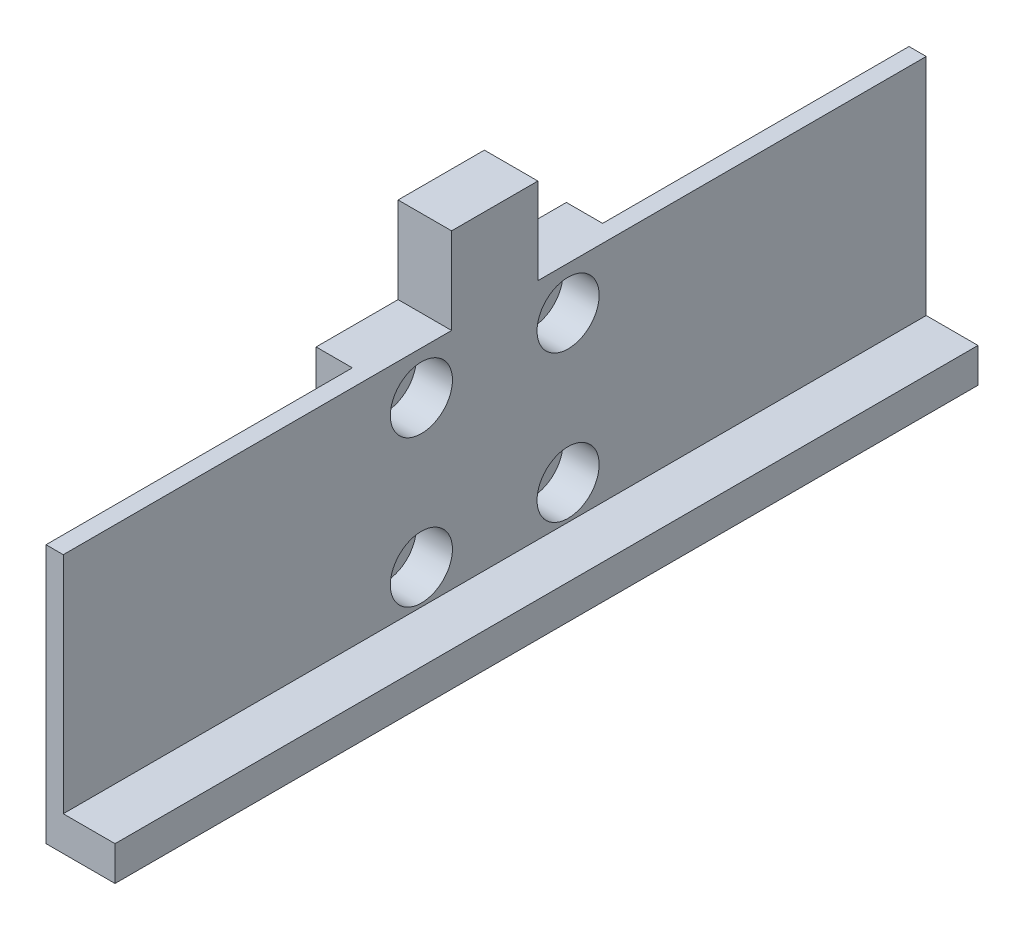
SolidWorks part; units mm, degrees
ref_plane "Front Plane" through (0, 0, 0) normal (0, 0, 1) x (1, 0, 0)
ref_plane "Top Plane" through (0, 0, 0) normal (0, 1, 0) x (1, 0, 0)
ref_plane "Right Plane" through (0, 0, 0) normal (1, 0, 0) x (0, 0, -1)
sketch "Sketch1" plane through (0, 0, 0) normal (1, 0, 0) x (0, 0, -1)
  line L1 (0, 0) -> (100, 0)
  line L2 (0, 0) -> (0, 26)
  line L3 (0, 26) -> (100, 26)
  line L4 (100, 0) -> (100, 26)
  dimension "D1" = 100
  dimension "D2" = 26
extrude "Boss-Extrude1" add sketch "Sketch1" along normal blind 2
sketch "Sketch2" plane through (0, 0, 0) normal (0, 0, 1) x (1, 0, 0)
  line L0 (2, 26) -> (2, 28)
  line L1 (2, 28) -> (-12, 28)
  line L2 (-12, 28) -> (-12, 24)
  line L3 (-12, 24) -> (-10, 24)
  line L4 (-10, 24) -> (-10, 26)
  line L5 (-10, 26) -> (2, 26)
  line L6 (2, 0) -> (0, 0) construction
  line L7 (0, 26) -> (0, 0) construction
  dimension "D1" = 10
  dimension "D2" = 2
extrude "Boss-Extrude2" add sketch "Sketch2" against normal up to surface (100 mm away) up to face at (1, 13, -100)
sketch "Sketch3" plane through (2, 0, 0) normal (1, 0, 0) x (0, 0, -1)
  line L0 (100, 28) -> (0, 28) construction
  line L1 (37.5, 28) -> (62.5, 28)
  line L2 (37.5, 28) -> (37.5, 0)
  line L3 (37.5, 0) -> (62.5, 0)
  line L4 (62.5, 28) -> (62.5, 0)
  line L5 (0, 0) -> (100, 0) construction
  point P8 (50, 0)
  point P9 (50, 28)
  dimension "D1" = 25
  dimension "D2" = 28
extrude "Boss-Extrude3" add sketch "Sketch3" along normal blind 4
sketch "Sketch4" plane through (6, 0, 0) normal (1, 0, 0) x (0, 0, -1)
  line L0 (62.5, 28) -> (37.5, 28) construction
  line L1 (41.5, 21) -> (58.5, 21) construction
  line L2 (41.5, 21) -> (41.5, 4) construction
  line L3 (41.5, 4) -> (58.5, 4) construction
  line L4 (58.5, 21) -> (58.5, 4) construction
  line L5 (37.5, 28) -> (37.5, 0) construction
  line L6 (37.5, 25) -> (62.5, 25) construction
  line L7 (37.5, 25) -> (37.5, 0) construction
  line L8 (37.5, 0) -> (62.5, 0) construction
  line L9 (62.5, 25) -> (62.5, 0) construction
  circle A0 centre (41.5, 21) radius 2.1
  circle A1 centre (58.5, 21) radius 2.1
  circle A2 centre (58.5, 4) radius 2.1
  circle A3 centre (41.5, 4) radius 2.1
  point P6 (50, 28)
  point P7 (50, 21)
  point P15 (62.5, 12.5)
  point P16 (58.5, 12.5)
  dimension "D2" = 25
  dimension "D3" = 4.2
  dimension "D1" = 17
extrude "Cut-Extrude1" cut sketch "Sketch4" against normal through all
mirror "Mirror1" about plane through (6, 0, 0) normal (1, 0, 0) of bodies 104
delete or keep bodies "Body-Delete/Keep 1" type delete bodies bodies 104
sketch "Sketch5" plane through (12, 0, 0) normal (1, 0, 0) x (0, 0, -1)
  line L0 (-10, 36) -> (-10, -10)
  line L1 (-10, -10) -> (110, -10)
  line L2 (110, -10) -> (110, 36)
  line L3 (110, 36) -> (-10, 36)
  line L4 (0, 26) -> (0, 0)
  line L5 (0, 0) -> (100, 0)
  line L6 (100, 0) -> (100, 26)
  line L7 (100, 26) -> (0, 26)
  line L8 (0, 26) -> (0, 0)
  line L9 (0, 0) -> (100, 0)
  line L10 (100, 0) -> (100, 26)
  line L11 (100, 26) -> (0, 26)
  dimension "D1" = 0
  dimension "D2" = 10
extrude "Cut-Extrude2" cut sketch "Sketch5" against normal through all both and the other way through all
sketch "Sketch6" plane through (12, 0, 0) normal (1, 0, 0) x (0, 0, -1)
  line L4 (0, 26) -> (0, 0)
  line L5 (0, 0) -> (100, 0)
  line L6 (100, 0) -> (100, 26)
  line L7 (100, 26) -> (0, 26)
  line L8 (0, 26) -> (0, 0)
  line L9 (0, 0) -> (100, 0)
  line L10 (100, 0) -> (100, 26)
  line L11 (100, 26) -> (0, 26)
  circle A0 centre (41.5, 21) radius 3.6
  circle A1 centre (58.5, 21) radius 3.6
  circle A2 centre (58.5, 4) radius 3.6
  circle A3 centre (41.5, 4) radius 3.6
  dimension "D2" = 7.2
  dimension "D1" = 0
extrude "Boss-Extrude4" add sketch "Sketch6" along normal blind 4.2
sketch "Sketch8" plane through (16.2, 0, 0) normal (1, 0, 0) x (0, 0, -1)
  line L0 (100, 0) -> (100, 26) construction
  line L1 (0, 0) -> (100, 0)
  line L2 (0, 0) -> (0, -4)
  line L3 (0, -4) -> (100, -4)
  line L4 (100, 0) -> (100, -4)
  dimension "D1" = 4
extrude "Boss-Extrude5" add sketch "Sketch8" along normal blind 6 separate body
sketch "Sketch9" plane through (16.2, 0, 0) normal (-1, 0, 0) x (0, 0, 1)
  line L4 (0, -4) -> (0, 0)
  line L5 (0, 0) -> (-100, 0)
  line L6 (-100, 0) -> (-100, -4)
  line L7 (-100, -4) -> (0, -4)
  line L8 (0, -4) -> (0, 0)
  line L9 (0, 0) -> (-100, 0)
  line L10 (-100, 0) -> (-100, -4)
  line L11 (-100, -4) -> (0, -4)
  dimension "D1" = 0
extrude "Boss-Extrude6" add sketch "Sketch9" along normal up to surface (10.2 mm away) up to face at (6, 4, -43.6)
sketch "Sketch10" plane through (0, 0, 0) normal (0, 1, 0) x (1, 0, 0)
  line L4 (6, 0) -> (10, 0)
  line L5 (10, 0) -> (10, 37.5)
  line L6 (10, 37.5) -> (6, 37.5)
  line L7 (6, 37.5) -> (6, 0)
  line L8 (6, 0) -> (10, 0)
  line L9 (10, 0) -> (10, 37.5)
  line L10 (10, 37.5) -> (6, 37.5)
  line L11 (6, 37.5) -> (6, 0)
  line L12 (6, 100) -> (6, 62.5)
  line L13 (6, 62.5) -> (10, 62.5)
  line L14 (10, 62.5) -> (10, 100)
  line L15 (10, 100) -> (6, 100)
  line L16 (6, 100) -> (6, 62.5)
  line L17 (6, 62.5) -> (10, 62.5)
  line L18 (10, 62.5) -> (10, 100)
  line L19 (10, 100) -> (6, 100)
  dimension "D1" = 0
  dimension "D2" = 0
extrude "Cut-Extrude3" cut sketch "Sketch10" against normal through all contours L18 L19 L16 L17 | L11 L8 L9 L10
sketch "Sketch11" plane through (0, 26, 0) normal (0, 1, 0) x (1, 0, 0)
  line L1 (6, 62.5) -> (10, 62.5)
  line L2 (6, 62.5) -> (6, 37.5)
  line L3 (6, 37.5) -> (10, 37.5)
  line L4 (10, 62.5) -> (10, 37.5)
extrude "Cut-Extrude4" cut sketch "Sketch11" against normal through all
sketch "Sketch13" plane through (10, 0, 0) normal (-1, 0, 0) x (0, 0, 1)
  line L0 (-100, 26) -> (0, 26) construction
  line L1 (-55, 26) -> (-45, 26)
  line L2 (-55, 26) -> (-55, 36)
  line L3 (-55, 36) -> (-45, 36)
  line L4 (-45, 26) -> (-45, 36)
  point P6 (-50, 26)
  point P7 (-50, 26)
  dimension "D1" = 10
  dimension "D2" = 10
extrude "Boss-Extrude7" add sketch "Sketch13" against normal up to surface (6.2 mm away) up to face at (16.2, 13, -50)
sketch "Sketch14" plane through (0, 26, 0) normal (0, 1, 0) x (1, 0, 0)
  line L0 (10, 0) -> (16.2, 0) construction
  line L1 (14.2, 0) -> (10, 0)
  line L2 (14.2, 0) -> (14.2, 35.5)
  line L3 (14.2, 35.5) -> (10, 35.5)
  line L4 (10, 0) -> (10, 35.5)
  line L5 (10, 45) -> (10, 0) construction
  line L7 (10, 100) -> (14.2, 100)
  line L8 (10, 100) -> (10, 64.5)
  line L9 (10, 64.5) -> (14.2, 64.5)
  line L10 (14.2, 100) -> (14.2, 64.5)
  dimension "D1" = 29
  dimension "D2" = 2
extrude "Cut-Extrude5" cut sketch "Sketch14" against normal through all
